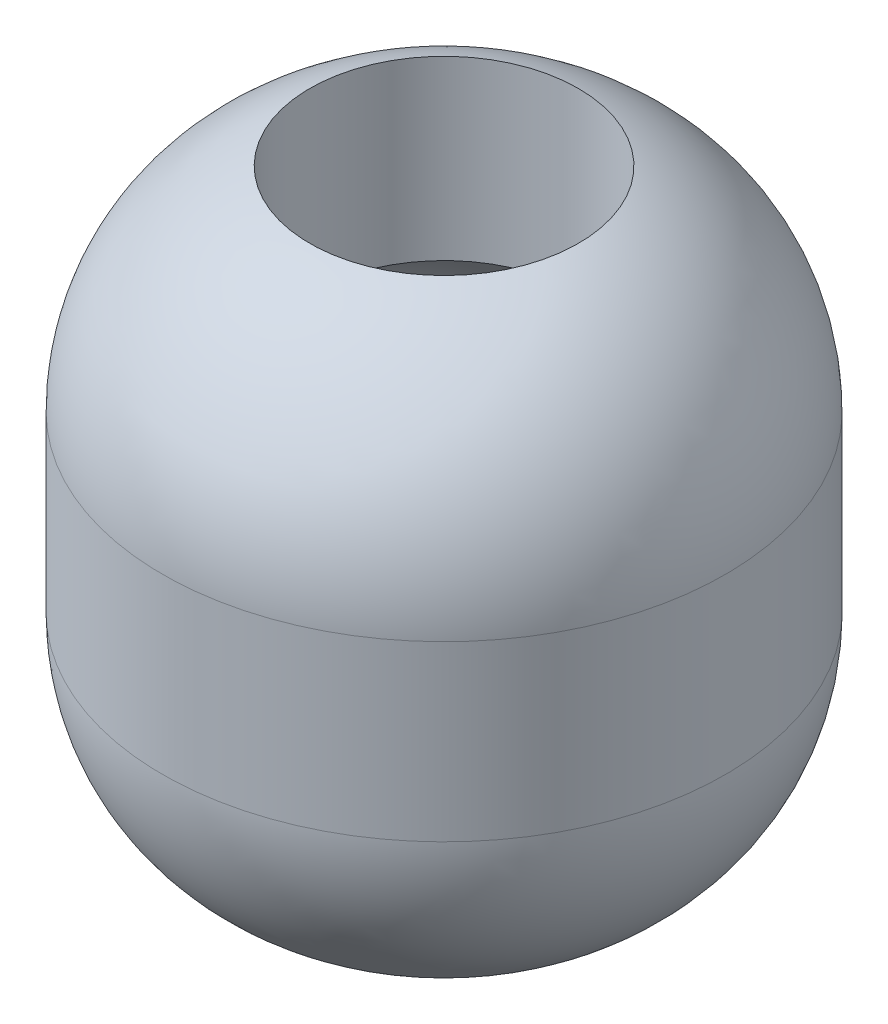
SolidWorks part; units mm, degrees
ref_plane "Ebene vorne" through (0, 0, 0) normal (0, 0, 1) x (1, 0, 0)
ref_plane "Ebene oben" through (0, 0, 0) normal (0, 1, 0) x (1, 0, 0)
ref_plane "Ebene rechts" through (0, 0, 0) normal (1, 0, 0) x (0, 0, -1)
sketch "Skizze1" plane through (0, 0, 0) normal (0, 0, 1) x (1, 0, 0)
  line L0 (0, 0) -> (0, 410) construction
  line L1 (-83.5, 410) -> (-83.5, 300)
  line L2 (-175, 277.5247) -> (-175, 169.7446)
  line L3 (-36, 140) -> (-36, 87)
  line L4 (-36, 87) -> (-94, 87)
  line L5 (-94, 87) -> (-116.4066, 55)
  arc A1 (-83.5, 410) -> (-175, 277.5247) centre (-33.35, 277.5247) ccw
  arc A3 (-163.5, 224) -> (-36, 140) centre (-33.35, 282.7857) ccw
  arc A4 (-83.5, 300) -> (-163.5, 224) centre (-33.35, 167.1053) ccw
  arc A6 (-175, 169.7446) -> (-116.4066, 55) centre (-33.35, 169.7446) ccw
  point P11 (0, 0)
  point P16 (-116.4066, 47.5122)
  dimension "D1" = 175
  dimension "D2" = 163.5
  dimension "D3" = 36
  dimension "D4" = 83.5
  dimension "D5" = 110
  dimension "D6" = 186
  dimension "D7" = 53
  dimension "D8" = 355
  dimension "D9" = 58
  dimension "D10" = 32
  dimension "D11" = 33.35
  dimension "D12" = 125
  dimension "D13" = 55
revolve "Rotation1" add sketch "Skizze1" angle 360 about L0
